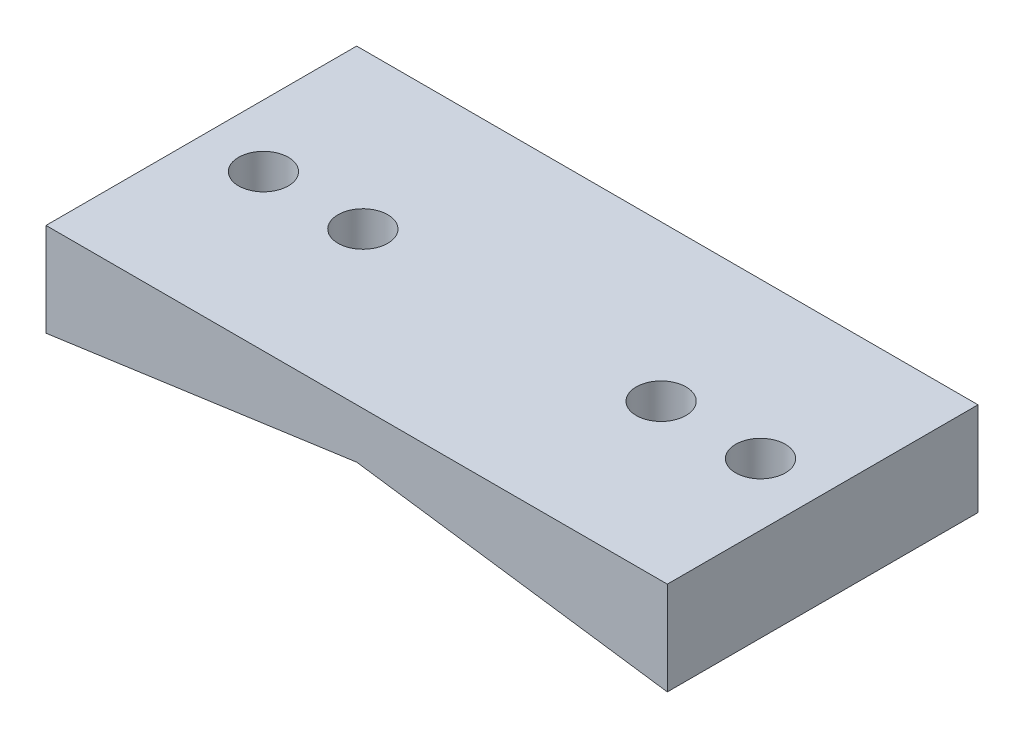
SolidWorks part; units mm, degrees
ref_plane "Plan de face" through (0, 0, 0) normal (0, 0, 1) x (1, 0, 0)
ref_plane "Plan de dessus" through (0, 0, 0) normal (0, 1, 0) x (1, 0, 0)
ref_plane "Plan de droite" through (0, 0, 0) normal (1, 0, 0) x (0, 0, -1)
sketch "Esquisse1" plane through (0, 0, 0) normal (0, 0, 1) x (1, 0, 0)
  line L4 (-50, -10) -> (50, -10)
  line L5 (-50, -10) -> (-50, 10)
  line L11 (50, -10) -> (50, 10)
  line L12 (-50, 10) -> (50, 10)
  line L13 (-50, -10) -> (50, 10) construction
  line L14 (50, -10) -> (-50, 10) construction
  point P1 (0, 0)
  dimension "D1" = 100
  dimension "D2" = 20
extrude "Boss.-Extru.1" add sketch "Esquisse1" along normal mid plane 50 contours L12 L11 L4 L5
hole_wizard "Fraisage pour vis à tête fraisée M81" positions "Esquisse12" profile "Esquisse13" countersink size "M8" standard "Ansi Metric" end condition through all
sketch "Esquisse12" plane through (0, -10, 0) normal (0, -1, 0) x (-1, 0, 0)
  point P0 (24, 0)
  point P2 (-24, 0)
sketch "Esquisse13" plane through (-24, -10, 0) normal (1, 0, 0) x (0, 0, -1)
  line L0 (0, 0) -> (0, 20)
  line L1 (0, 20) -> (4, 20)
  line L2 (4, 20) -> (4, 14)
  line L3 (4, 14) -> (8, 10)
  line L4 (8, 10) -> (8, 0)
  line L6 (8, 0) -> (0, 0)
  line L7 (-4, 14) -> (-8, 10) construction
  line L11 (0, -6.35) -> (0, 107.95) construction
  dimension "Diamètre du perçage jusqu'au prochain" = 8
  dimension "Profondeur du perçage jusqu'au prochain" = 20
  dimension "Diamètre du fraisage" = 16
  dimension "Angle du fraisage" = 90
  dimension "Dégagement de la tête" = 10
hole_wizard "Diamètre du perçage Ø8.0 (8)1" positions "Esquisse14" profile "Esquisse15" hole size "Ø8.0" standard "Ansi Metric" end condition through all
sketch "Esquisse14" plane through (0, -10, 0) normal (0, -1, 0) x (-1, 0, 0)
  point P0 (-40, 0)
  point P2 (40, 0)
sketch "Esquisse15" plane through (40, -10, 0) normal (1, 0, 0) x (0, 0, -1)
  line L0 (0, 0) -> (0, 20)
  line L1 (0, 20) -> (4, 20)
  line L2 (4, 20) -> (4, 0)
  line L5 (4, 0) -> (0, 0)
  line L11 (0, -6.35) -> (0, 107.95) construction
  dimension "Diamètre du perçage jusqu'au prochain" = 8
  dimension "Profondeur du perçage jusqu'au prochain" = 20
sketch "Esquisse16" plane through (0, 0, -25) normal (0, 0, -1) x (-1, 0, 0)
  line L0 (0, 2) -> (-50, -5.027)
  line L1 (-50, -10) -> (-50, 10) construction
  line L2 (-50, -5.027) -> (-50, -10)
  line L3 (-50, -10) -> (50, -10)
  line L4 (50, -10) -> (50, -5.027)
  line L5 (50, -10) -> (50, 10) construction
  line L6 (50, -5.027) -> (0, 2)
  line L7 (50, 10) -> (-50, 10) construction
  point P14 (0, 0)
  point P15 (0, 15.1765)
extrude "Enlèv. mat.-Extru.1" cut sketch "Esquisse16" against normal through all contours L6 L0 L2 L3 L4
equation "\"D2@Esquisse12\"=\"D1@Esquisse12\"/2"
equation "\"D2@Esquisse14\"=\"D1@Esquisse14\"/2"
equation "\"D2@Esquisse16\"=\"D1@Esquisse16\""
